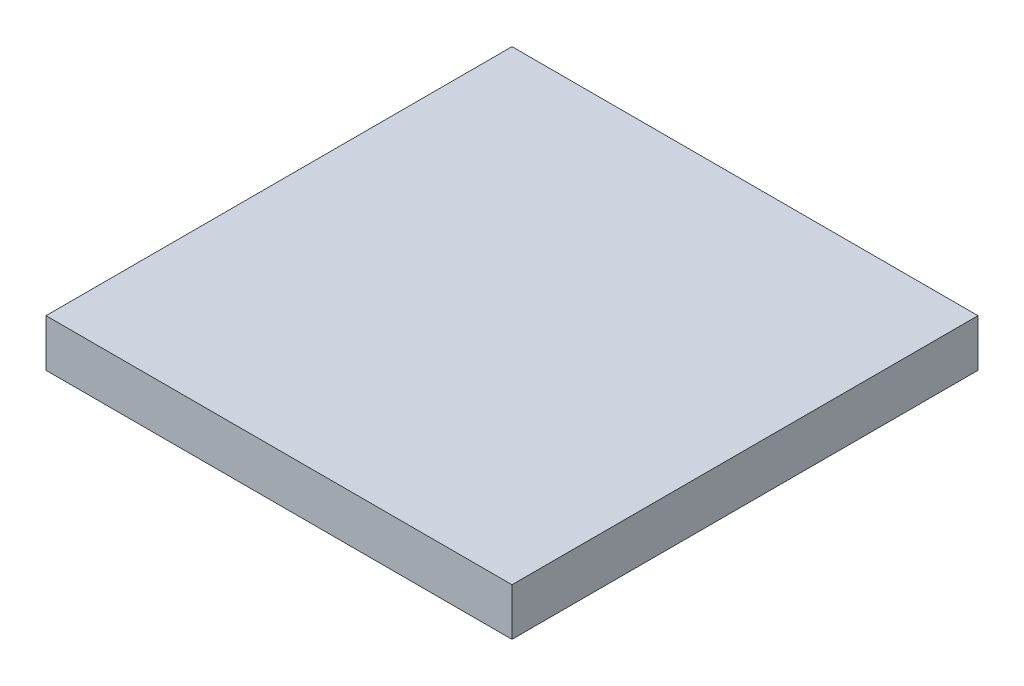
SolidWorks part; units mm, degrees
ref_plane "Front Plane" through (0, 0, 0) normal (0, 0, 1) x (1, 0, 0)
ref_plane "Top Plane" through (0, 0, 0) normal (0, 1, 0) x (1, 0, 0)
ref_plane "Right Plane" through (0, 0, 0) normal (1, 0, 0) x (0, 0, -1)
sketch "Sketch1" plane through (0, 0, 0) normal (0, 1, 0) x (1, 0, 0)
  line L1 (-16.764, -2.54) -> (16.764, -2.54)
  line L2 (-16.764, -2.54) -> (-16.764, 2.54)
  line L3 (-16.764, 2.54) -> (16.764, 2.54)
  line L4 (16.764, -2.54) -> (16.764, 2.54)
  line L5 (-16.764, -2.54) -> (16.764, 2.54) construction
  line L6 (-16.764, 2.54) -> (16.764, -2.54) construction
  point P0 (0, 0)
extrude "Boss-Extrude1" add sketch "Sketch1" along normal blind 13.97
sketch "Sketch2" plane through (0, 13.97, 0) normal (0, 1, 0) x (1, 0, 0)
  line L1 (-16.764, 2.54) -> (33.236, 2.54)
  line L2 (-16.764, 2.54) -> (-16.764, -47.46)
  line L3 (-16.764, -47.46) -> (33.236, -47.46)
  line L4 (33.236, 2.54) -> (33.236, -47.46)
extrude "Boss-Extrude2" add sketch "Sketch2" along normal blind 5.08
